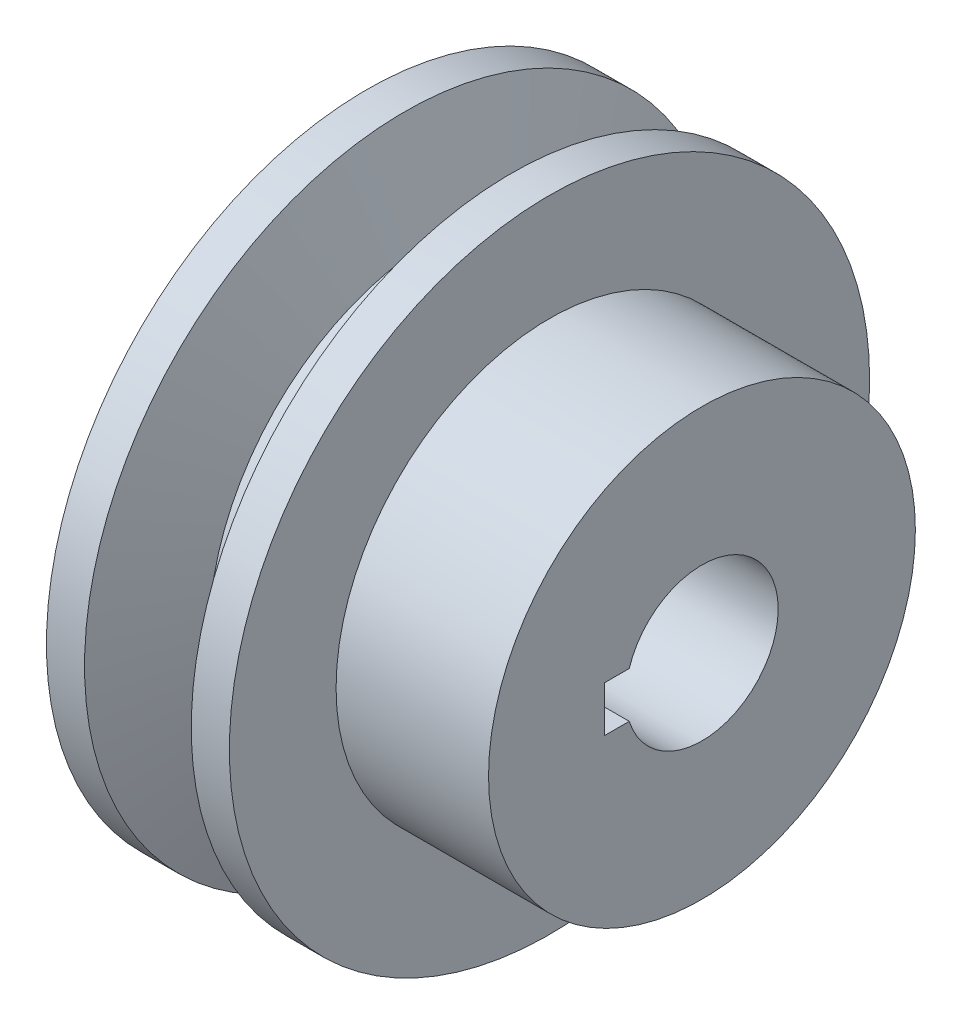
SolidWorks part; units mm, degrees
ref_plane "Front Plane" through (0, 0, 0) normal (0, 0, 1) x (1, 0, 0)
ref_plane "Top Plane" through (0, 0, 0) normal (0, 1, 0) x (1, 0, 0)
ref_plane "Right Plane" through (0, 0, 0) normal (1, 0, 0) x (0, 0, -1)
sketch "Sketch1" plane through (0, 0, 0) normal (0, 0, 1) x (1, 0, 0)
  line L0 (22, 0) -> (0, 0)
  line L1 (0, 0) -> (0, 21)
  line L2 (0, 21) -> (2.5, 21)
  line L3 (2.5, 21) -> (4.6838, 15)
  line L4 (4.6838, 15) -> (7.3162, 15)
  line L5 (7.3162, 15) -> (9.5, 21)
  line L6 (9.5, 21) -> (12, 21)
  line L7 (12, 21) -> (12, 14)
  line L8 (12, 14) -> (22, 14)
  line L9 (22, 14) -> (22, 0)
  line L10 (6, 15) -> (6, 21.4414) construction
  dimension "D1" = 22
  dimension "D2" = 12
  dimension "D3" = 40
  dimension "D4" = 7
  dimension "D5" = 21
  dimension "D6" = 14
  dimension "D7" = 15
revolve "Revolve1" add sketch "Sketch1" angle 360 about L0
sketch "Sketch2" plane through (0, 0, 0) normal (-1, 0, 0) x (0, 0, 1)
  line L0 (0, 0) -> (13.7799, 0) construction
  line L1 (6.4, 1.5) -> (6.4, -1.5)
  line L2 (6.4, -1.5) -> (4.7697, -1.5)
  line L3 (6.4, 1.5) -> (4.7697, 1.5)
  arc A0 (4.7697, 1.5) -> (4.7697, -1.5) centre (0, 0) ccw
  dimension "D1" = 10
  dimension "D2" = 6.4
  dimension "D3" = 3
  dimension "D4" = 1.5
extrude "Cut-Extrude1" cut sketch "Sketch2" against normal through all
